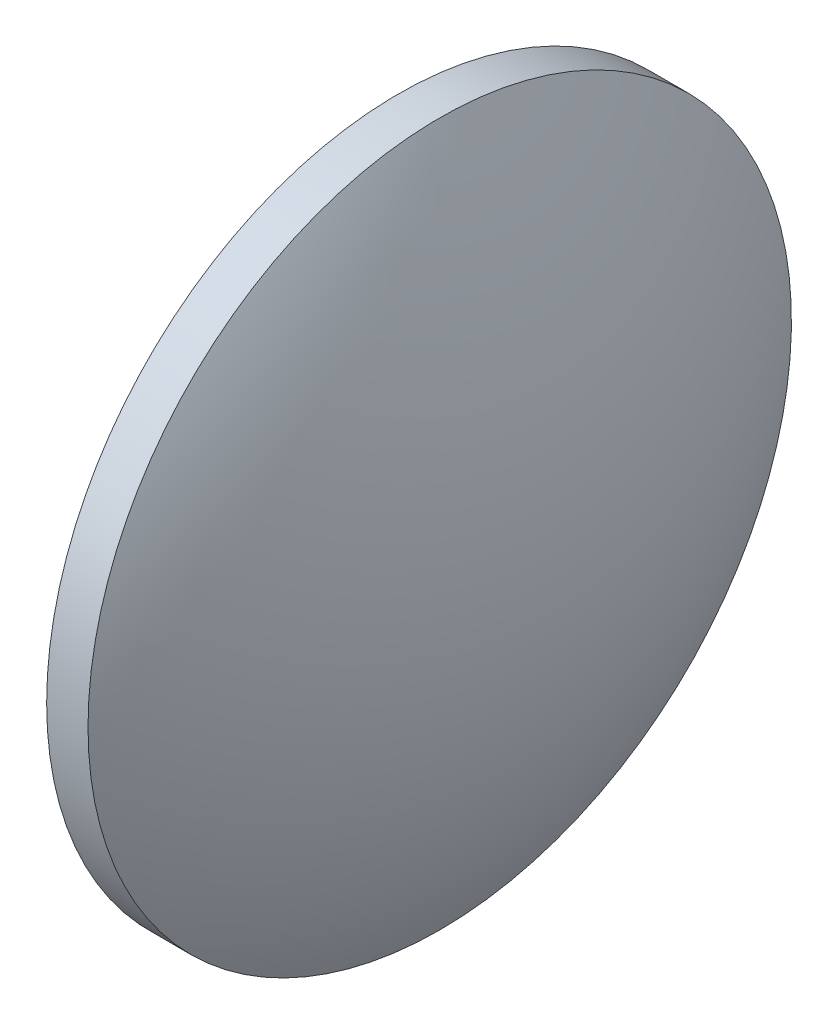
SolidWorks part; units mm, degrees
ref_plane "前视基准面" through (0, 0, 0) normal (0, 0, 1) x (1, 0, 0)
ref_plane "上视基准面" through (0, 0, 0) normal (0, 1, 0) x (1, 0, 0)
ref_plane "右视基准面" through (0, 0, 0) normal (1, 0, 0) x (0, 0, -1)
sketch "草图1" plane through (0, 0, 0) normal (0, 0, 1) x (1, 0, 0)
  line L0 (552.5002, 36.8937) -> (562.0882, 36.8937) construction
  line L1 (554.8658, 36.8937) -> (554.8658, 49.3937)
  line L2 (554.8658, 49.3937) -> (556.3358, 49.3937)
  line L3 (559.5658, 36.8937) -> (554.8658, 36.8937)
  arc A0 (559.5658, 36.8937) -> (556.3358, 49.3937) centre (533.7635, 36.8937) ccw
revolve "旋转1" add sketch "草图1" angle 360 about L0
